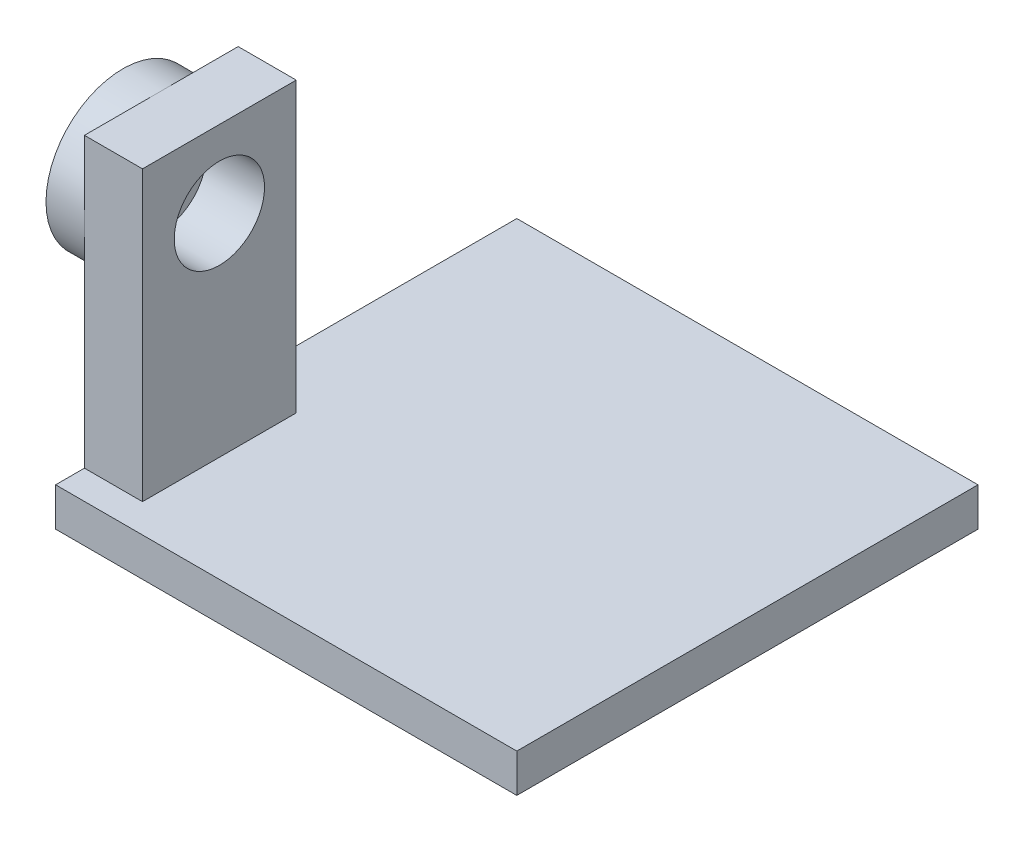
SolidWorks part; units mm, degrees
ref_plane "Front Plane" through (0, 0, 0) normal (0, 0, 1) x (1, 0, 0)
ref_plane "Top Plane" through (0, 0, 0) normal (0, 1, 0) x (1, 0, 0)
ref_plane "Right Plane" through (0, 0, 0) normal (1, 0, 0) x (0, 0, -1)
sketch "Sketch3" plane through (0, 0, 0) normal (0, 1, 0) x (1, 0, 0)
  line L1 (-27.9712, 13.4245) -> (-3.9712, 13.4245)
  line L2 (-27.9712, 13.4245) -> (-27.9712, -10.5755)
  line L3 (-27.9712, -10.5755) -> (-3.9712, -10.5755)
  line L4 (-3.9712, 13.4245) -> (-3.9712, -10.5755)
  dimension "D1" = 24
  dimension "D2" = 24
extrude "Boss-Extrude1" add sketch "Sketch3" along normal blind 2
sketch "Sketch4" plane through (0, 2, 0) normal (0, 1, 0) x (1, 0, 0)
  line L0 (-3.9712, 13.4245) -> (-27.9712, 13.4245) construction
  line L1 (-27.9712, -1.0755) -> (-24.9492, -1.0755)
  line L2 (-27.9712, -1.0755) -> (-27.9712, -9.0755)
  line L3 (-27.9712, -9.0755) -> (-24.9492, -9.0755)
  line L4 (-24.9492, -1.0755) -> (-24.9492, -9.0755)
  line L5 (-27.9712, -1.0755) -> (-24.9492, -9.0755) construction
  line L6 (-27.9712, -9.0755) -> (-24.9492, -1.0755) construction
  line L8 (-27.9712, 13.4245) -> (-27.9712, -10.5755) construction
  point P0 (-26.4602, -5.0755)
  dimension "D1" = 14.5
  dimension "D2" = 8
  dimension "D3" = 0
extrude "Boss-Extrude2" add sketch "Sketch4" along normal blind 15
ref_plane "Plane1" through (-27.9712, 17, 1.0755) normal (0, 0, 1) x (1, 0, 0)
sketch "Sketch6" plane through (-24.9492, 0, 0) normal (1, 0, 0) x (0, 0, -1)
  line L0 (-1.0755, 17) -> (-1.0755, 2) construction
  line L1 (-9.0755, 17) -> (-1.0755, 17) construction
  circle A0 centre (-5.0755, 13) radius 2.35
  dimension "D3" = 4.7
  dimension "D1" = 4
  dimension "D2" = 4
extrude "Cut-Extrude1" cut sketch "Sketch6" against normal blind 3.2
sketch "Sketch7" plane through (-27.9712, 0, 0) normal (-1, 0, 0) x (0, 0, 1)
  circle A0 centre (5.0755, 13) radius 4
  dimension "D1" = 8
extrude "Boss-Extrude3" add sketch "Sketch7" along normal blind 2
sketch "Sketch8" plane through (-29.9712, 0, 0) normal (-1, 0, 0) x (0, 0, 1)
  circle A0 centre (5.0755, 13) radius 1
  dimension "D1" = 2
extrude "Cut-Extrude2" cut sketch "Sketch8" against normal blind 2
sketch "Sketch9" plane through (-29.9712, 0, 0) normal (-1, 0, 0) x (0, 0, 1)
  circle A0 centre (5.0755, 13) radius 1.25
  dimension "D1" = 2.5
extrude "Cut-Extrude3" cut sketch "Sketch9" against normal blind 0.3
